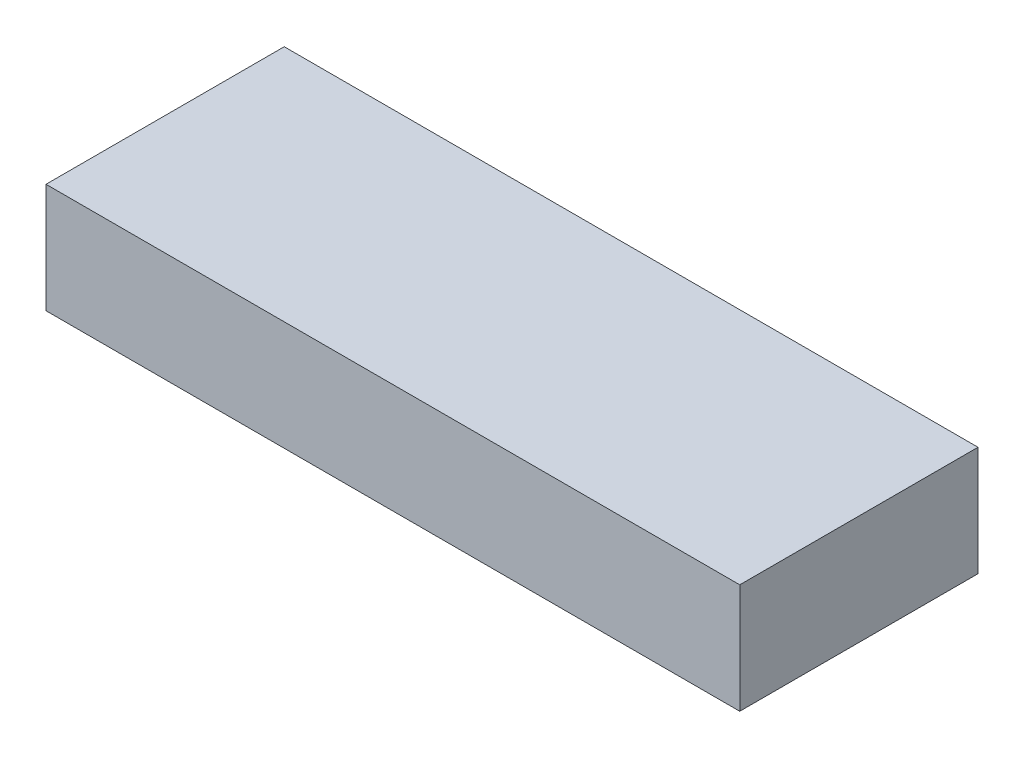
SolidWorks part; units mm, degrees
ref_plane "Front Plane" through (0, 0, 0) normal (0, 0, 1) x (1, 0, 0)
ref_plane "Top Plane" through (0, 0, 0) normal (0, 1, 0) x (1, 0, 0)
ref_plane "Right Plane" through (0, 0, 0) normal (1, 0, 0) x (0, 0, -1)
sketch "Sketch1" plane through (0, 0, 0) normal (0, 1, 0) x (1, 0, 0)
  line L1 (0, 0) -> (19.304, 0)
  line L2 (0, 0) -> (0, 6.6294)
  line L3 (0, 6.6294) -> (19.304, 6.6294)
  line L4 (19.304, 0) -> (19.304, 6.6294)
  dimension "D1" = 19.304
  dimension "D2" = 6.6294
extrude "Boss-Extrude1" add sketch "Sketch1" along normal blind 3.048
